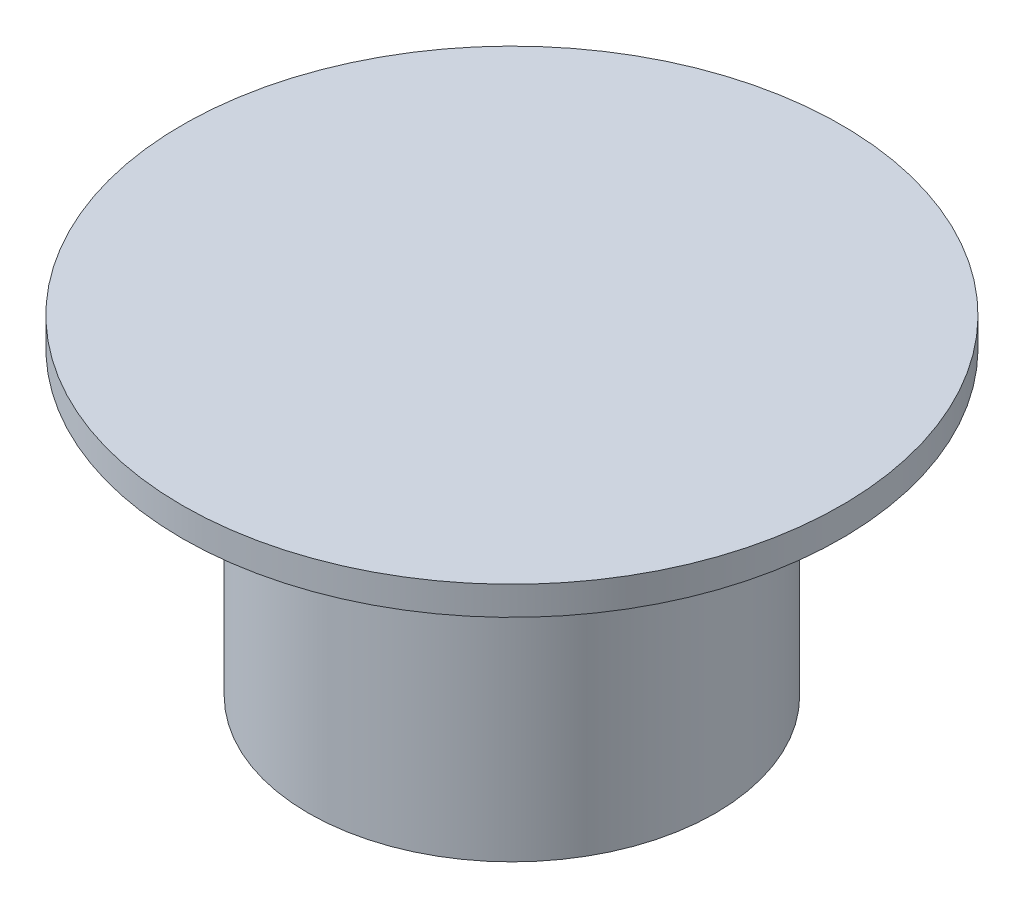
SolidWorks part; units mm, degrees
ref_plane "Front Plane" through (0, 0, 0) normal (0, 0, 1) x (1, 0, 0)
ref_plane "Top Plane" through (0, 0, 0) normal (0, 1, 0) x (1, 0, 0)
ref_plane "Right Plane" through (0, 0, 0) normal (1, 0, 0) x (0, 0, -1)
sketch "Sketch1" plane through (0, 0, 0) normal (0, 1, 0) x (1, 0, 0)
  circle A0 centre (0, 0) radius 7.1
extrude "Boss-Extrude1" add sketch "Sketch1" along normal blind 10.5
sketch "Sketch2" plane through (0, 10.5, 0) normal (0, 1, 0) x (1, 0, 0)
  circle A0 centre (0, 0) radius 11.5
extrude "Boss-Extrude2" add sketch "Sketch2" along normal blind 1
sketch "Sketch3" plane through (0, 0, 0) normal (0, -1, 0) x (1, 0, 0)
  line L1 (-2.5, 1.5) -> (2.5, 1.5)
  line L2 (-2.5, 1.5) -> (-2.5, -1.5)
  line L3 (-2.5, -1.5) -> (2.5, -1.5)
  line L4 (2.5, 1.5) -> (2.5, -1.5)
  dimension "D1" = 5
  dimension "D2" = 3
  dimension "D3" = 2.5
  dimension "D4" = 1.5
extrude "Cut-Extrude1" cut sketch "Sketch3" against normal blind 6
